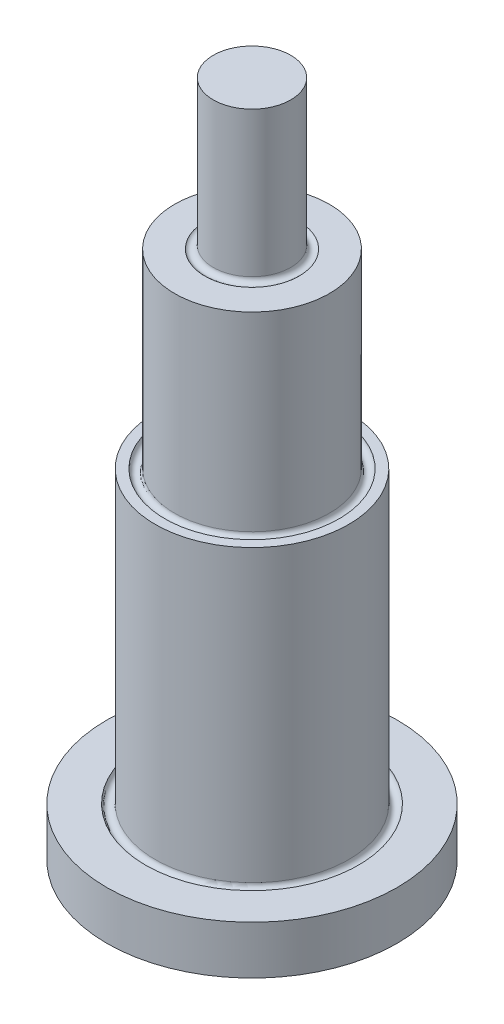
SolidWorks part; units mm, degrees
ref_plane "Front Plane" through (0, 0, 0) normal (0, 0, 1) x (1, 0, 0)
ref_plane "Top Plane" through (0, 0, 0) normal (0, 1, 0) x (1, 0, 0)
ref_plane "Right Plane" through (0, 0, 0) normal (1, 0, 0) x (0, 0, -1)
sketch "Sketch1" plane through (0, 0, 0) normal (0, 0, 1) x (1, 0, 0)
  line L0 (-9, 0) -> (-10, 0)
  line L2 (0, 0) -> (0, -30)
  line L4 (-10, 0) -> (-10, -30)
  line L5 (-11, -30) -> (-15, -30)
  line L6 (0, -30) -> (0, -35)
  line L7 (0, -35) -> (-15, -35)
  line L8 (-15, -30) -> (-15, -35)
  line L10 (0, 0) -> (0, 20)
  line L12 (-8, 0) -> (-8, 19.6655)
  line L13 (0, 20) -> (0, 35)
  line L14 (0, 35) -> (-4, 35)
  line L15 (-4, 35) -> (-4, 20)
  line L16 (-4.8716, 19.6655) -> (-8, 19.6655)
  arc A0 (-9, 0) -> (-8, 0) centre (-8.5, 0) ccw
  arc A1 (-11, -30) -> (-10, -30) centre (-10.5, -30) ccw
  arc A2 (-4.8716, 19.6655) -> (-4, 20) centre (-4.5, 20) ccw
  dimension "D6" = 1
  dimension "D7" = 1
  dimension "D9" = 1
  dimension "D1" = 10
  dimension "D2" = 15
  dimension "D3" = 15
  dimension "D4" = 5
  dimension "D5" = 8
  dimension "D8" = 4
  dimension "D10" = 0
  dimension "D11" = 20
revolve "Revolve1" add sketch "Sketch1" angle 360 about L10
